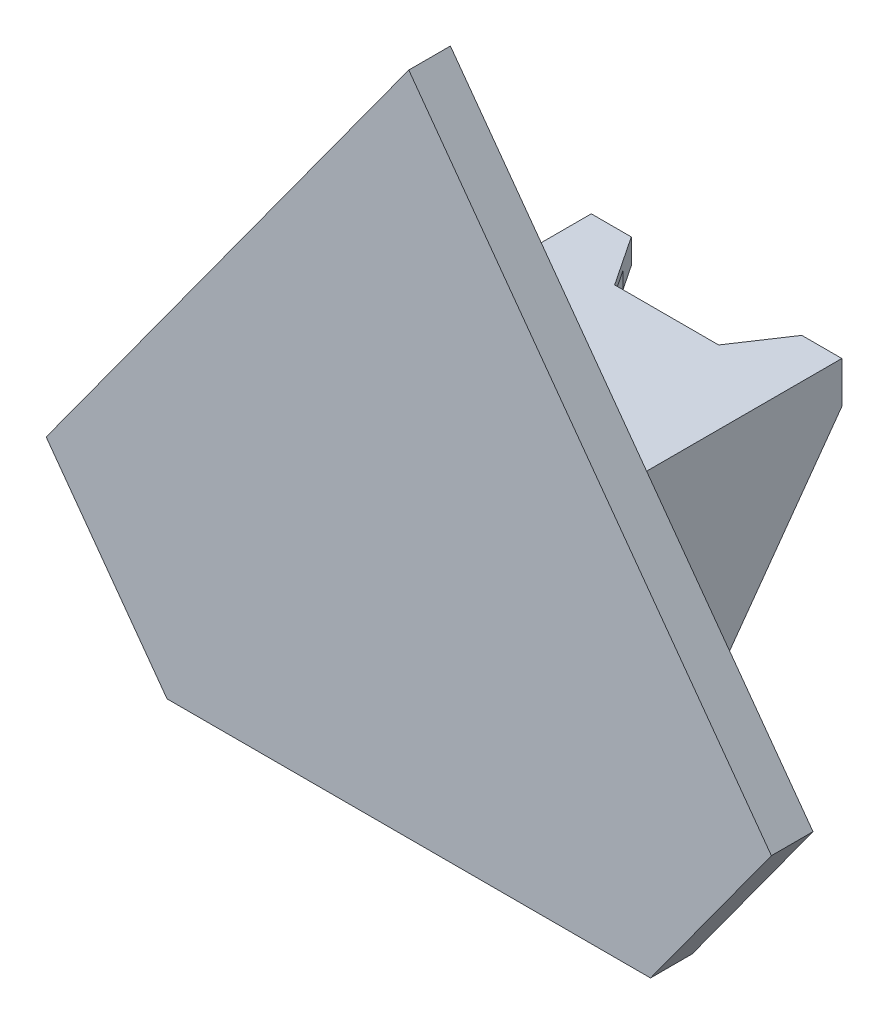
SolidWorks part; units mm, degrees
ref_plane "Front Plane" through (0, 0, 0) normal (0, 0, 1) x (1, 0, 0)
ref_plane "Top Plane" through (0, 0, 0) normal (0, 1, 0) x (1, 0, 0)
ref_plane "Right Plane" through (0, 0, 0) normal (1, 0, 0) x (0, 0, -1)
sketch "Sketch2" plane through (0, 0, 0) normal (0, 1, 0) x (1, 0, 0)
  line L0 (15.061, 0) -> (15.061, 32)
  line L1 (-12.561, 2.5) -> (12.561, 2.5)
  line L2 (-12.561, 2.5) -> (-12.561, 32)
  line L4 (12.561, 2.5) -> (12.561, 32)
  line L5 (15.061, 32) -> (12.561, 32)
  line L7 (-15.061, 32) -> (-15.061, 0)
  line L8 (-15.061, 0) -> (15.061, 0)
  line L10 (-15.061, 32) -> (-12.561, 32)
  point P4 (0, 2.5)
  point P12 (0, 0)
  dimension "D1" = 2.5
  dimension "D2" = 2.5
  dimension "D3" = 29.5
  dimension "D4" = 25.122
extrude "Boss-Extrude1" add sketch "Sketch2" along normal blind 32.5
sketch "Sketch4" plane through (0, 0, 0) normal (0, -1, 0) x (1, 0, 0)
  line L4 (-7.5, -6) -> (7.5, -6)
  line L9 (15.061, 0) -> (-15.061, 0)
  line L13 (-12.561, -2.5) -> (-12.561, -32) construction
  line L18 (-12.561, -10) -> (-7.5, -6)
  line L23 (12.561, -32) -> (12.561, -2.5) construction
  line L26 (12.561, -10) -> (7.5, -6)
  line L32 (-12.561, -10) -> (-15.061, -10)
  line L33 (-15.061, -32) -> (-15.061, 0) construction
  line L34 (-15.061, -10) -> (-15.061, 0)
  line L35 (12.561, -10) -> (15.061, -10)
  line L36 (15.061, 0) -> (15.061, -32) construction
  line L37 (15.061, -10) -> (15.061, 0)
  circle A2 centre (-10.2499, -4.95) radius 1.05
  circle A5 centre (10.2499, -4.95) radius 1.05
  point P31 (0, -6)
  dimension "D5" = 2.1
  dimension "D10" = 15
  dimension "D11" = 10
  dimension "D2" = 6
  dimension "D7" = 4.95
extrude "Boss-Extrude2" add sketch "Sketch4" along normal blind 2.5
sketch "Sketch5" plane through (0, 32.5, 0) normal (0, 1, 0) x (1, 0, 0)
  line L0 (-15.061, 32) -> (-10.2499, 32)
  line L9 (-10.2499, 32) -> (-6.25, 26)
  line L13 (-15.061, 0) -> (15.061, 0) construction
  line L14 (15.061, 0) -> (-15.061, 0)
  line L15 (-15.061, 0) -> (-15.061, 32)
  line L20 (15.061, 0) -> (15.061, 32)
  line L21 (-6.25, 26) -> (6.25, 26)
  line L22 (6.25, 26) -> (10.2499, 32)
  line L23 (10.2499, 32) -> (15.061, 32)
  circle A0 centre (-10.2499, 4.95) radius 1.05 construction
  circle A1 centre (-10.2499, 8.7) radius 1.05
  circle A2 centre (10.2499, 8.7) radius 1.05
  point P6 (0, 26)
  dimension "D4" = 0
  dimension "D1" = 8.7
  dimension "D2" = 12.5
  dimension "D3" = 20.4998
  dimension "D5" = 6
extrude "Boss-Extrude3" add sketch "Sketch5" along normal blind 3
sketch "Sketch6" plane through (-15.061, 0, 0) normal (-1, 0, 0) x (0, 0, 1)
  line L0 (-10, 0) -> (-32, 30.5)
  line L1 (-32, 30.5) -> (-32, 0)
  line L2 (-32, 0) -> (-10, 0)
  line L3 (-32, 35.5) -> (-32, 0) construction
  dimension "D1" = 5
extrude "Cut-Extrude1" cut sketch "Sketch6" against normal through all
ref_plane "Plane1" through (0, 16.5, 0) normal (0, -1, 0) x (-1, 0, 0)
sketch "Sketch8" plane through (0, 0, 0) normal (0, 0, 1) x (1, 0, 0)
  line L0 (0, 76.5) -> (43.5926, 16.5)
  line L1 (-16.5671, 16.5) -> (16.5671, 16.5) construction
  line L2 (43.5926, 16.5) -> (-43.5926, 16.5)
  line L3 (-43.5926, 16.5) -> (0, 76.5)
  dimension "D1" = 72
  dimension "D2" = 60
extrude "Boss-Extrude4" add sketch "Sketch8" along normal blind 5
sketch "Sketch9" plane through (0, 0, 0) normal (0, 0, 1) x (1, 0, 0)
  line L0 (-43.5926, 16.5) -> (-58.1234, -3.5)
  line L1 (-58.1234, -3.5) -> (58.1234, -3.5)
  line L2 (58.1234, -3.5) -> (43.5926, 16.5)
  line L3 (-43.5926, 16.5) -> (43.5926, 16.5)
  line L4 (0, 76.5) -> (-43.5926, 16.5) construction
  line L5 (43.5926, 16.5) -> (0, 76.5) construction
  dimension "D1" = 20
extrude "Boss-Extrude6" add sketch "Sketch9" along normal up to surface (5 mm away) up to face at (0, 36.5, 5)
sketch "Sketch10" plane through (0, 0, 0) normal (0, 0, -1) x (-1, 0, 0)
  line L0 (-29.0617, -3.5) -> (-43.5926, 16.5)
  line L1 (58.1234, -3.5) -> (-58.1234, -3.5) construction
  line L2 (-58.1234, -3.5) -> (0, 76.5) construction
  line L3 (-43.5926, 16.5) -> (-58.1234, -3.5)
  line L4 (-58.1234, -3.5) -> (-29.0617, -3.5)
  line L5 (58.1234, -3.5) -> (43.5926, 16.5)
  line L13 (0, 76.5) -> (58.1234, -3.5) construction
  line L14 (43.5926, 16.5) -> (29.0617, -3.5)
  line L15 (58.1234, -3.5) -> (-58.1234, -3.5) construction
  line L16 (29.0617, -3.5) -> (58.1234, -3.5)
  point P13 (43.5926, -3.5)
  dimension "D1" = 20
extrude "Cut-Extrude2" cut sketch "Sketch10" against normal through all
sketch "Sketch12" plane through (0, 0, -26) normal (0, 0, -1) x (-1, 0, 0)
  line L1 (-8.2499, 34.5) -> (8.2499, 34.5)
  line L2 (-8.2499, 34.5) -> (-8.2499, 32.5)
  line L3 (-8.2499, 32.5) -> (8.2499, 32.5)
  line L4 (8.2499, 34.5) -> (8.2499, 32.5)
  line L5 (6.25, 32.5) -> (10.2499, 32.5) construction
  line L6 (-10.2499, 35.5) -> (-6.25, 35.5) construction
  point P8 (-8.2499, 35.5)
  dimension "D1" = 2
extrude "Cut-Extrude4" cut sketch "Sketch12" against normal up to surface (23.5 mm away) and the other way blind 10 up to face at (0, 16.25, -2.5)
